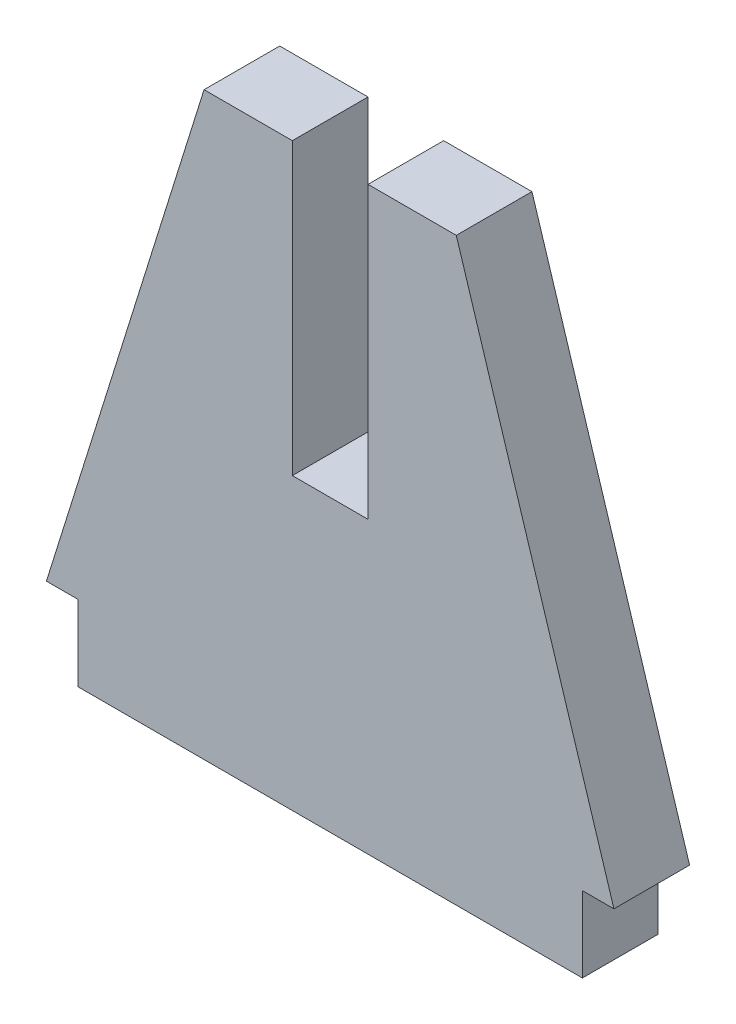
SolidWorks part; units mm, degrees
ref_plane "Front Plane" through (0, 0, 0) normal (0, 0, 1) x (1, 0, 0)
ref_plane "Top Plane" through (0, 0, 0) normal (0, 1, 0) x (1, 0, 0)
ref_plane "Right Plane" through (0, 0, 0) normal (1, 0, 0) x (0, 0, -1)
sketch "Sketch1" plane through (0, 0, 0) normal (0, 0, 1) x (1, 0, 0)
  line L0 (-20, 0) -> (20, 0)
  line L1 (20, 0) -> (20, 6)
  line L2 (-10, 46) -> (-22.5, 6)
  line L3 (10, 46) -> (-10, 46)
  line L4 (-22.5, 6) -> (-20, 6)
  line L5 (-20, 6) -> (-20, 0)
  line L6 (0, 46) -> (0, 0) construction
  line L7 (10, 46) -> (22.5, 6)
  line L8 (22.5, 6) -> (20, 6)
  dimension "D1" = 6
  dimension "D2" = 40
  dimension "D3" = 40
  dimension "D4" = 20
  dimension "D5" = 45
extrude "Boss-Extrude1" add sketch "Sketch1" along normal mid plane 6
sketch "Sketch2" plane through (0, 0, 3) normal (0, 0, 1) x (1, 0, 0)
  line L0 (10, 46) -> (-10, 46) construction
  line L1 (-3, 46) -> (3, 46)
  line L2 (-3, 46) -> (-3, 23)
  line L3 (-3, 23) -> (3, 23)
  line L4 (3, 46) -> (3, 23)
  line L5 (0, 23) -> (0, 0) construction
  dimension "D1" = 6
extrude "Cut-Extrude1" cut sketch "Sketch2" against normal through all
